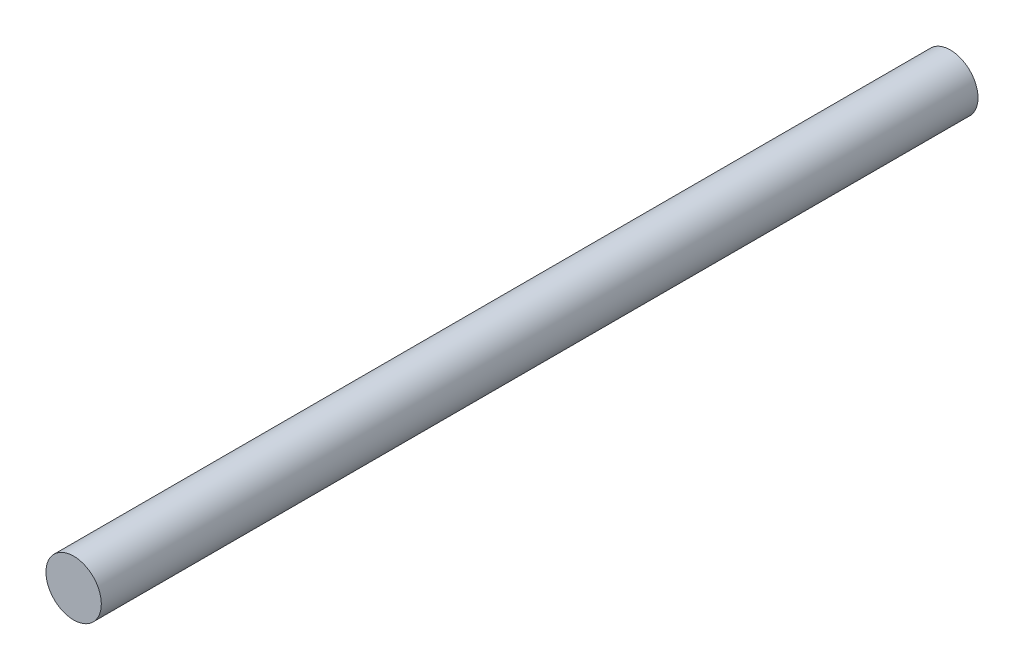
SolidWorks part; units mm, degrees
material "4032-T6"
ref_plane "Front Plane" through (0, 0, 0) normal (0, 0, 1) x (1, 0, 0)
ref_plane "Top Plane" through (0, 0, 0) normal (0, 1, 0) x (1, 0, 0)
ref_plane "Right Plane" through (0, 0, 0) normal (1, 0, 0) x (0, 0, -1)
sketch "Sketch1" plane through (0, 0, 0) normal (0, 0, 1) x (1, 0, 0)
  circle A0 centre (0, 0) radius 6
  dimension "D1" = 12
extrude "Boss-Extrude1" add sketch "Sketch1" along normal blind 190
